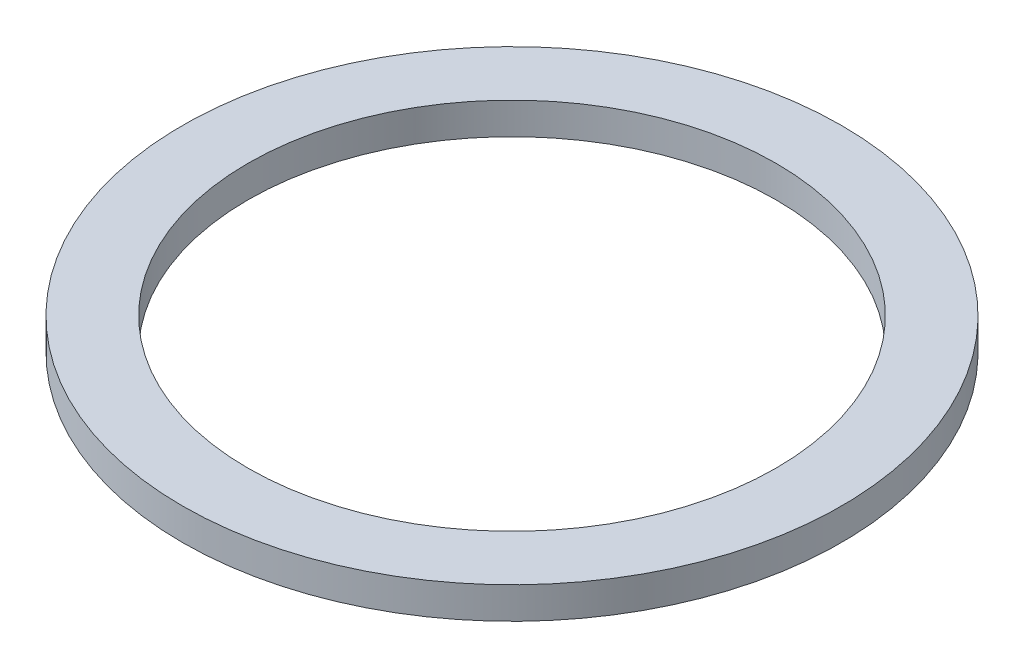
SolidWorks part; units mm, degrees
ref_plane "Front Plane" through (0, 0, 0) normal (0, 0, 1) x (1, 0, 0)
ref_plane "Top Plane" through (0, 0, 0) normal (0, 1, 0) x (1, 0, 0)
ref_plane "Right Plane" through (0, 0, 0) normal (1, 0, 0) x (0, 0, -1)
sketch "Sketch2" plane through (0, 0, 0) normal (0, 1, 0) x (1, 0, 0)
  circle A0 centre (0, 0) radius 49.55
  circle A1 centre (0, 0) radius 39.7
  dimension "D1" = 99.1
  dimension "D2" = 79.4
extrude "Boss-Extrude1" add sketch "Sketch2" along normal blind 4.7625
